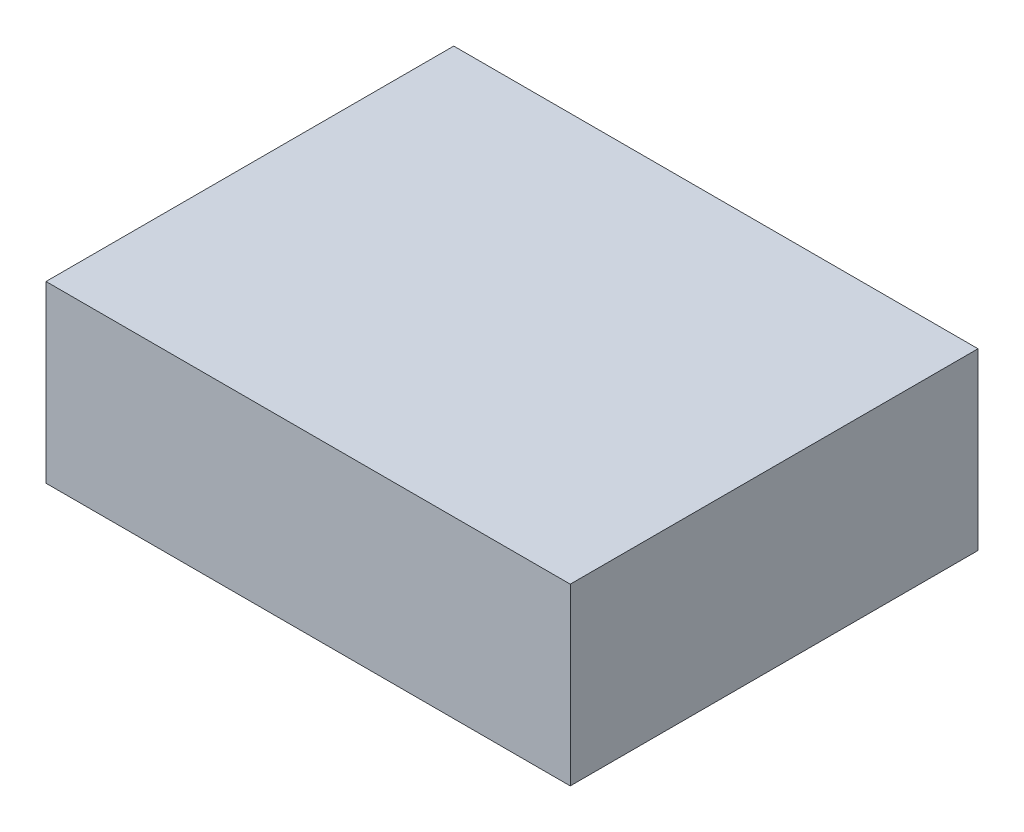
SolidWorks part; units mm, degrees
ref_plane "Front Plane" through (0, 0, 0) normal (0, 0, 1) x (1, 0, 0)
ref_plane "Top Plane" through (0, 0, 0) normal (0, 1, 0) x (1, 0, 0)
ref_plane "Right Plane" through (0, 0, 0) normal (1, 0, 0) x (0, 0, -1)
sketch "Sketch1" plane through (0, 0, 0) normal (0, 1, 0) x (1, 0, 0)
  line L1 (0, 0) -> (114.3, 0)
  line L2 (0, 0) -> (0, 88.9)
  line L3 (0, 88.9) -> (114.3, 88.9)
  line L4 (114.3, 0) -> (114.3, 88.9)
  dimension "D1" = 88.9
  dimension "D2" = 114.3
extrude "Boss-Extrude1" add sketch "Sketch1" along normal blind 38.1
